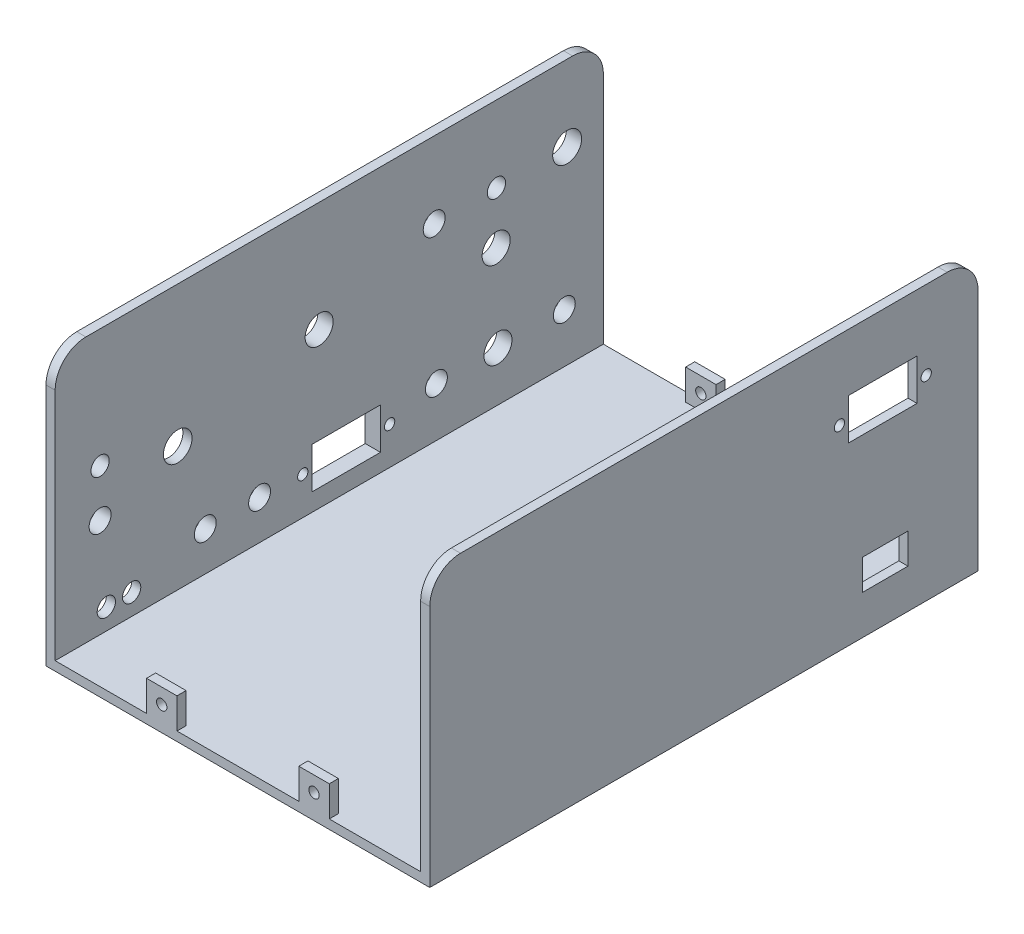
SolidWorks part; units mm, degrees
ref_plane "Front Plane" through (0, 0, 0) normal (0, 0, 1) x (1, 0, 0)
ref_plane "Top Plane" through (0, 0, 0) normal (0, 1, 0) x (1, 0, 0)
ref_plane "Right Plane" through (0, 0, 0) normal (1, 0, 0) x (0, 0, -1)
sketch "Sketch1" plane through (0, 0, 0) normal (0, 0, 1) x (1, 0, 0)
  line L1 (0, 0) -> (126, 0)
  line L2 (0, 0) -> (0, -90)
  line L3 (0, -90) -> (126, -90)
  line L4 (126, 0) -> (126, -90)
  dimension "D1" = 90
  dimension "D2" = 126
extrude "Boss-Extrude1" add sketch "Sketch1" along normal blind 3
sketch "Sketch2" plane through (0, 0, 0) normal (0, 0, -1) x (-1, 0, 0)
  line L0 (-126, -90) -> (-126, 0)
  line L1 (-126, 0) -> (0, 0)
  line L2 (0, 0) -> (0, -90)
  line L3 (0, -90) -> (-3, -90)
  line L4 (0, -90) -> (-126, -90) construction
  line L5 (-3, -90) -> (-3, -3)
  line L6 (-3, -3) -> (-123, -3)
  line L7 (-123, -3) -> (-123, -90)
  line L8 (-123, -90) -> (-126, -90)
  dimension "D1" = 3
  dimension "D2" = 3
  dimension "D3" = 3
extrude "Boss-Extrude2" add sketch "Sketch2" against normal blind 177
sketch "Sketch3" plane through (0, 0, 177) normal (0, 0, 1) x (1, 0, 0)
  line L5 (0, 0) -> (126, 0)
  line L6 (0, 0) -> (0, -90)
  line L7 (0, -90) -> (126, -90)
  line L8 (126, 0) -> (126, -90)
extrude "Boss-Extrude3" add sketch "Sketch3" along normal blind 3
fillet "Fillet1" radius 10 4 edges at (63, -3, 177) (63, 0, 180) (63, -3, 3) (63, 0, 0)
sketch "Sketch4" plane through (0, 0, 0) normal (-1, 0, 0) x (0, 0, 1)
  line L0 (0, -10) -> (0, -90) construction
  line L1 (60, -60) -> (10, -60)
  line L2 (60, -60) -> (60, -10)
  line L3 (60, -10) -> (10, -10)
  line L4 (10, -60) -> (10, -10)
  line L5 (10, -65) -> (60, -65)
  line L6 (10, -65) -> (10, -80)
  line L7 (10, -80) -> (60, -80)
  line L8 (60, -65) -> (60, -80)
  line L9 (70, -10) -> (120, -10)
  line L10 (70, -10) -> (70, -60)
  line L11 (70, -60) -> (120, -60)
  line L12 (120, -10) -> (120, -60)
  line L13 (70, -65) -> (100, -65)
  line L14 (70, -65) -> (70, -80)
  line L15 (70, -80) -> (100, -80)
  line L16 (100, -65) -> (100, -80)
  line L17 (105, -65) -> (120, -65)
  line L18 (105, -65) -> (105, -80)
  line L19 (105, -80) -> (120, -80)
  line L20 (120, -65) -> (120, -80)
  line L21 (135, -10) -> (165, -10)
  line L22 (135, -10) -> (135, -23.8915)
  line L23 (135, -23.8915) -> (165, -23.8915)
  line L24 (165, -10) -> (165, -23.8915)
  line L25 (130, -30.8764) -> (167, -30.8764)
  line L26 (130, -30.8764) -> (130, -55.8764)
  line L27 (130, -55.8764) -> (167, -55.8764)
  line L28 (167, -30.8764) -> (167, -55.8764)
  line L35 (170, 0) -> (10, 0) construction
  line L36 (180, -90) -> (0, -90) construction
  line L37 (180, -10) -> (180, -90) construction
  point P33 (135, -16.9458)
  dimension "D1" = 50
  dimension "D2" = 50
  dimension "D3" = 50
  dimension "D4" = 50
  dimension "D5" = 50
  dimension "D6" = 30
  dimension "D7" = 15
  dimension "D8" = 37
  dimension "D9" = 10
  dimension "D10" = 10
  dimension "D11" = 15
  dimension "D12" = 10
  dimension "D13" = 10
  dimension "D14" = 10
  dimension "D15" = 15
  dimension "D16" = 15
  dimension "D17" = 25
sketch "Sketch5" plane through (-2, 0, 0) normal (-1, 0, 0) x (0, 0, 1)
  line L0 (180, -10) -> (180, -90) construction
  circle A11 centre (154.8799, -80.1094) radius 3
  circle A12 centre (163.2002, -80.1094) radius 3
  dimension "D1" = 16.7998
extrude "Cut-Extrude1" cut sketch "Sketch5" against normal blind 5
sketch "Sketch6" plane through (126, 0, 0) normal (1, 0, 0) x (0, 0, -1)
  line L0 (0, -90) -> (0, -10) construction
  line L1 (-20, -32.3454) -> (-42.5, -32.3454)
  line L2 (-20, -32.3454) -> (-20, -18.8454)
  line L3 (-20, -18.8454) -> (-42.5, -18.8454)
  line L4 (-42.5, -32.3454) -> (-42.5, -18.8454)
  line L5 (-38, -67.1252) -> (-23, -67.1252)
  line L6 (-38, -67.1252) -> (-38, -77.1252)
  line L7 (-38, -77.1252) -> (-23, -77.1252)
  line L8 (-23, -67.1252) -> (-23, -77.1252)
  dimension "D1" = 22.5
  dimension "D2" = 13.5
  dimension "D3" = 20
  dimension "D4" = 10
  dimension "D5" = 15
  dimension "D6" = 23
extrude "Cut-Extrude2" cut sketch "Sketch6" against normal blind 3
sketch "Sketch7" plane through (0, -90, 0) normal (0, -1, 0) x (-1, 0, 0)
  line L5 (0, -180) -> (-180, -180)
  line L6 (0, -180) -> (0, 0)
  line L7 (0, 0) -> (-180, 0)
  line L8 (-180, -180) -> (-180, 0)
  dimension "D1" = 180
extrude "Boss-Extrude5" add sketch "Sketch7" against normal blind 3
sketch "Sketch8" plane through (0, 0, 0) normal (-1, 0, 0) x (0, 0, 1)
  line L0 (0, -79.8987) -> (0, -90)
  line L5 (10.1013, 0) -> (169.8987, 0)
  line L6 (0, -10.1013) -> (0, -79.8987)
  line L7 (10.1013, -90) -> (169.8987, -90)
  line L8 (180, -10.1013) -> (180, -79.8987)
  line L13 (0, -90) -> (10.1013, -90)
  line L14 (169.8987, -90) -> (180, -90)
  line L15 (180, -90) -> (180, -79.8987)
  arc A1 (10.1013, 0) -> (0, -10.1013) centre (10.1013, -10.1013) ccw
  arc A2 (169.8987, 0) -> (180, -10.1013) centre (169.8987, -10.1013) cw
  point P12 (0, 0)
  point P17 (180, -90)
extrude "Cut-Extrude3" cut sketch "Sketch8" against normal through all flip side to cut
sketch "Sketch9" plane through (0, 0, 0) normal (0, 0, -1) x (-1, 0, 0)
  line L1 (-123, 0) -> (-3, 0)
  line L2 (-123, 0) -> (-123, -87)
  line L3 (-123, -87) -> (-3, -87)
  line L4 (-3, 0) -> (-3, -87)
  line L5 (-126, -87) -> (-126, -10.1013) construction
  line L6 (0, -10.1013) -> (0, -90) construction
  line L7 (-180, -90) -> (0, -90) construction
  dimension "D1" = 3
  dimension "D2" = 3
  dimension "D3" = 3
  dimension "D4" = 87
extrude "Cut-Extrude4" cut sketch "Sketch9" against normal through all
sketch "Sketch11" plane through (0, -87, 0) normal (0, 1, 0) x (1, 0, 0)
  line L0 (123, -180) -> (3, -180) construction
  line L9 (33, -180) -> (43, -180)
  line L10 (33, -180) -> (33, -177)
  line L11 (33, -177) -> (43, -177)
  line L12 (43, -180) -> (43, -177)
  line L13 (123, 0) -> (3, 0) construction
  line L14 (83, -180) -> (93, -180)
  line L15 (83, -180) -> (83, -177)
  line L16 (83, -177) -> (93, -177)
  line L17 (93, -180) -> (93, -177)
  line L18 (33, 0) -> (43, 0)
  line L19 (33, 0) -> (33, -3)
  line L20 (33, -3) -> (43, -3)
  line L21 (43, 0) -> (43, -3)
  line L22 (3, -180) -> (3, 0) construction
  line L23 (83, 0) -> (93, 0)
  line L24 (83, 0) -> (83, -3)
  line L25 (83, -3) -> (93, -3)
  line L26 (93, 0) -> (93, -3)
  line L27 (123, 0) -> (123, -180) construction
  point P20 (43, -178.5)
  point P23 (93, -178.5)
  dimension "D1" = 3
  dimension "D2" = 3
  dimension "D3" = 3
  dimension "D4" = 3
  dimension "D5" = 10
  dimension "D6" = 10
  dimension "D7" = 10
  dimension "D8" = 10
  dimension "D9" = 30
  dimension "D10" = 30
  dimension "D11" = 40
  dimension "D12" = 30
  dimension "D13" = 30
extrude "Boss-Extrude6" add sketch "Sketch11" along normal blind 10
sketch "Sketch12" plane through (0, 0, 0) normal (0, 0, -1) x (-1, 0, 0)
  line L0 (-93, -77) -> (-93, -87) construction
  line L1 (-93, -77) -> (-83, -77) construction
  line L2 (-43, -77) -> (-43, -87) construction
  line L3 (-43, -77) -> (-33, -77) construction
  circle A1 centre (-88, -82) radius 1.7
  circle A2 centre (-38, -82) radius 1.7
  dimension "D1" = 5
  dimension "D2" = 5
  dimension "D3" = 5
  dimension "D4" = 5
extrude "Cut-Extrude5" cut sketch "Sketch12" against normal blind 10
sketch "Sketch13" plane through (0, 0, 180) normal (0, 0, 1) x (1, 0, 0)
  line L0 (33, -77) -> (33, -87) construction
  line L1 (33, -77) -> (43, -77) construction
  line L2 (83, -77) -> (83, -87) construction
  line L3 (83, -77) -> (93, -77) construction
  circle A0 centre (38, -82) radius 1.7
  circle A1 centre (88, -82) radius 1.7
  dimension "D1" = 5
  dimension "D2" = 5
  dimension "D3" = 5
  dimension "D4" = 5
extrude "Cut-Extrude6" cut sketch "Sketch13" against normal blind 10
sketch "Sketch14" plane through (3, 0, 0) normal (1, 0, 0) x (0, 0, -1)
  line L1 (-42.6204, -21) -> (-27.6204, -21) construction
  line L2 (-42.6204, -21) -> (-42.6204, -29) construction
  line L3 (-42.6204, -29) -> (-27.6204, -29) construction
  line L4 (-27.6204, -21) -> (-27.6204, -29) construction
  line L5 (-50.7016, -29.5503) -> (-19.7016, -29.5503) construction
  line L6 (-50.7016, -29.5503) -> (-50.7016, -54.5503) construction
  line L7 (-50.7016, -54.5503) -> (-19.7016, -54.5503) construction
  line L8 (-19.7016, -29.5503) -> (-19.7016, -54.5503) construction
  line L9 (-46.3264, -55.2522) -> (-21.3264, -55.2522) construction
  line L10 (-46.3264, -55.2522) -> (-46.3264, -86.2522) construction
  line L11 (-46.3264, -86.2522) -> (-21.3264, -86.2522) construction
  line L12 (-21.3264, -55.2522) -> (-21.3264, -86.2522) construction
  line L13 (-42.6204, -21) -> (-27.6204, -21)
  line L14 (-42.6204, -21) -> (-42.6204, -29)
  line L15 (-42.6204, -29) -> (-27.6204, -29)
  line L16 (-27.6204, -21) -> (-27.6204, -29)
  line L17 (-46.3264, -55.2522) -> (-21.3264, -55.2522)
  line L18 (-46.3264, -55.2522) -> (-46.3264, -86.2522)
  line L19 (-46.3264, -86.2522) -> (-21.3264, -86.2522)
  line L20 (-21.3264, -55.2522) -> (-21.3264, -86.2522)
  line L21 (-50.7016, -29.5503) -> (-19.7016, -29.5503)
  line L22 (-50.7016, -29.5503) -> (-50.7016, -54.5503)
  line L23 (-50.7016, -54.5503) -> (-19.7016, -54.5503)
  line L24 (-19.7016, -29.5503) -> (-19.7016, -54.5503)
  line L25 (-172.7432, -34.9908) -> (-157.7432, -34.9908)
  line L26 (-172.7432, -34.9908) -> (-172.7432, -42.9908)
  line L27 (-172.7432, -42.9908) -> (-157.7432, -42.9908)
  line L28 (-157.7432, -34.9908) -> (-157.7432, -42.9908)
  line L34 (-73.1878, -67.6661) -> (-95.6878, -67.6661)
  line L35 (-73.1878, -67.6661) -> (-73.1878, -81.1661)
  line L36 (-73.1878, -81.1661) -> (-95.6878, -81.1661)
  line L37 (-95.6878, -67.6661) -> (-95.6878, -81.1661)
  line L38 (-180, -90) -> (0, -90) construction
  line L39 (-105.8166, -20.6885) -> (-80.8166, -20.6885)
  line L40 (-105.8166, -20.6885) -> (-105.8166, -51.6885)
  line L41 (-105.8166, -51.6885) -> (-80.8166, -51.6885)
  line L42 (-80.8166, -20.6885) -> (-80.8166, -51.6885)
  line L43 (-103.1878, -66.9931) -> (-65.1878, -66.9931)
  line L44 (-103.1878, -66.9931) -> (-103.1878, -81.9931)
  line L45 (-103.1878, -81.9931) -> (-65.1878, -81.9931)
  line L46 (-65.1878, -66.9931) -> (-65.1878, -81.9931)
  line L47 (0, -87) -> (0, -10.1013) construction
  circle A1 centre (-11.8978, -25) radius 11.25 construction
  circle A2 centre (-55.5472, -25) radius 8.5 construction
  circle A3 centre (-12.8264, -70.7522) radius 8.5 construction
  circle A4 centre (-54.8264, -70.7522) radius 8.5 construction
  circle A5 centre (-11.8978, -25) radius 11.1
  circle A6 centre (-55.5472, -25) radius 8.5
  circle A7 centre (-54.8264, -70.7522) radius 8.5
  circle A8 centre (-12.8264, -70.7522) radius 8.5
  circle A9 centre (-112.8727, -74.1268) radius 8.5
  circle A10 centre (-130.7113, -74.1268) radius 8.5
  circle A11 centre (-165.2432, -54.5503) radius 8.5
  circle A12 centre (-139.7536, -46.1677) radius 11.15
  point P78 (-165.2432, -42.9908)
  dimension "D1" = 15
  dimension "D3" = 17
  dimension "D8" = 38
  dimension "D13" = 15
  dimension "D20" = 22.2
  dimension "D21" = 17
  dimension "D22" = 17
  dimension "D23" = 22.3
  dimension "D24" = 17
  dimension "D25" = 17
  dimension "D26" = 17
  dimension "D27" = 17
  dimension "D2" = 8
  dimension "D4" = 31
  dimension "D5" = 25
  dimension "D6" = 31
  dimension "D7" = 25
  dimension "D9" = 7.5
  dimension "D10" = 25
  dimension "D11" = 21
  dimension "D12" = 15
  dimension "D14" = 8
  dimension "D15" = 22.5
  dimension "D16" = 13.5
  dimension "D17" = 3.7478
  dimension "D18" = 25
  dimension "D19" = 31
  dimension "D28" = 15.5
  dimension "D29" = 12.8264
  dimension "D30" = 8.5
  dimension "D31" = 8.5
sketch "Sketch16" plane through (-2, 0, 0) normal (-1, 0, 0) x (0, 0, 1)
  line L0 (0, -10.1013) -> (0, -90) construction
  line L5 (3.3978, -7) -> (63.3978, -7)
  line L6 (3.3978, -7) -> (3.3978, -52)
  line L7 (3.3978, -52) -> (63.3978, -52)
  line L8 (63.3978, -7) -> (63.3978, -52)
  line L9 (6.25, -55) -> (61.3865, -55)
  line L10 (6.25, -55) -> (6.25, -85)
  line L11 (6.25, -85) -> (61.3865, -85)
  line L12 (61.3865, -55) -> (61.3865, -85)
  line L13 (68.5355, -8) -> (118.5355, -8)
  line L14 (68.5355, -8) -> (68.5355, -53)
  line L15 (68.5355, -53) -> (118.5355, -53)
  line L16 (118.5355, -8) -> (118.5355, -53)
  line L17 (63.1467, -55) -> (120.8778, -55)
  line L18 (63.1467, -55) -> (63.1467, -85)
  line L19 (63.1467, -85) -> (120.8778, -85)
  line L20 (120.8778, -55) -> (120.8778, -85)
  line L21 (123.3103, -54.9622) -> (137.9052, -54.9622)
  line L22 (123.3103, -54.9622) -> (123.3103, -84.9622)
  line L23 (123.3103, -84.9622) -> (137.9052, -84.9622)
  line L24 (137.9052, -54.9622) -> (137.9052, -84.9622)
  line L25 (152.6969, -26.1054) -> (177.6096, -26.1054)
  line L26 (152.6969, -26.1054) -> (152.6969, -62.5896)
  line L27 (152.6969, -62.5896) -> (177.6096, -62.5896)
  line L28 (177.6096, -26.1054) -> (177.6096, -62.5896)
  line L29 (180, -90) -> (0, -90) construction
  line L30 (169.8987, 0) -> (10.1013, 0) construction
  circle A1 centre (11.8978, -25) radius 11.25 construction
  point P12 (130.6078, -84.9622)
  dimension "D1" = 60
  dimension "D2" = 8.5
  dimension "D3" = 6.25
  dimension "D4" = 55
  dimension "D5" = 5
  dimension "D6" = 5
  dimension "D7" = 45
  dimension "D8" = 30
  dimension "D9" = 50
  dimension "D10" = 45
  dimension "D11" = 7
  dimension "D12" = 8
  dimension "D13" = 30
extrude "Boss-Extrude7" add sketch "Sketch16" against normal blind 5
sketch "Sketch15" plane through (-2, 0, 0) normal (-1, 0, 0) x (0, 0, 1)
  line L0 (46.3264, -86.2522) -> (21.3264, -86.2522) construction
  line L1 (27.6204, -21) -> (27.6204, -29) construction
  line L2 (73.1878, -67.6661) -> (95.6878, -67.6661)
  line L3 (73.1878, -67.6661) -> (73.1878, -81.1661)
  line L4 (73.1878, -81.1661) -> (95.6878, -81.1661)
  line L5 (95.6878, -67.6661) -> (95.6878, -81.1661)
  line L10 (19.7016, -29.5503) -> (19.7016, -54.5503) construction
  line L11 (50.7016, -54.5503) -> (19.7016, -54.5503) construction
  line L13 (80.8166, -20.6885) -> (80.8166, -51.6885) construction
  line L14 (172.7432, -42.9908) -> (157.7432, -42.9908) construction
  line L16 (157.7432, -34.9908) -> (157.7432, -42.9908) construction
  circle A0 centre (11.8978, -25) radius 4.75
  circle A1 centre (35.1204, -25) radius 3
  circle A2 centre (55.5472, -25) radius 3.6
  circle A3 centre (93.3166, -36.1885) radius 4.6
  circle A4 centre (12.8264, -70.7522) radius 3.6
  circle A5 centre (54.8264, -70.7522) radius 3.6
  circle A6 centre (34.6032, -70.7522) radius 4.6
  circle A7 centre (35.2016, -42.0503) radius 4.6
  circle A8 centre (112.8727, -74.1268) radius 3.6
  circle A9 centre (130.7113, -74.1268) radius 3.6
  circle A10 centre (139.7536, -46.1677) radius 4.7
  circle A11 centre (165.2432, -54.5503) radius 3.6
  circle A12 centre (165.2432, -38.9908) radius 3
  circle A14 centre (11.8978, -25) radius 11.1 construction
  circle A15 centre (55.5472, -25) radius 8.5 construction
  circle A16 centre (12.8264, -70.7522) radius 8.5 construction
  circle A17 centre (54.8264, -70.7522) radius 8.5 construction
  circle A18 centre (112.8727, -74.1268) radius 8.5 construction
  circle A19 centre (130.7113, -74.1268) radius 8.5 construction
  circle A20 centre (139.7536, -46.1677) radius 11.15 construction
  circle A21 centre (165.2432, -54.5503) radius 8.5 construction
  point P48 (27.6204, -25)
  point P54 (19.7016, -42.0503)
  point P78 (80.8166, -36.1885)
  dimension "D1" = 7.2
  dimension "D2" = 13.5
  dimension "D3" = 15.5
  dimension "D4" = 12.5
  dimension "D5" = 15.5
  dimension "D6" = 12.5
  dimension "D7" = 4
  dimension "D8" = 7.5
  dimension "D11" = 21.7768
  dimension "D12" = 20.2232
extrude "Cut-Extrude7" cut sketch "Sketch15" against normal mid plane 15
fillet "Fillet3" radius 2.27 24 edges at (-1, -26.1054, 152.6969) (-1, -26.1054, 177.6096) (-1, -62.5896, 177.6096) (-1, -62.5896, 152.6969) (-1, -84.9622, 123.3103) (-1, -84.9622, 137.9052) (-1, -54.9622, 123.3103) (-1, -54.9622, 137.9052) (-1, -55, 120.8778) (-1, -85, 120.8778) (-1, -85, 63.1467) (-1, -85, 61.3865) (-1, -85, 6.25) (-1, -55, 6.25) (-1, -55, 63.1467) (-1, -55, 61.3865) (-1, -52, 63.3978) (-1, -52, 3.3978) (-1, -53, 68.5355) (-1, -53, 118.5355) (-1, -8, 118.5355) (-1, -8, 68.5355) (-1, -7, 63.3978) (-1, -7, 3.3978)
sketch "Sketch17" plane through (0, -87, 0) normal (0, 1, 0) x (1, 0, 0)
  line L1 (126, 0) -> (180, 0)
  line L2 (126, 0) -> (126, -180)
  line L3 (126, -180) -> (180, -180)
  line L4 (180, 0) -> (180, -180)
extrude "Cut-Extrude8" cut sketch "Sketch17" against normal blind 10
sketch "Sketch18" plane through (0, 0, 0) normal (-1, 0, 0) x (0, 0, 1)
  line L0 (180, -10.1013) -> (180, -90) construction
  line L5 (129, -5) -> (171, -5)
  line L6 (125, -9) -> (125, -19)
  line L7 (129, -23) -> (171, -23)
  line L8 (175, -9) -> (175, -19)
  line L9 (169.8987, 0) -> (10.1013, 0) construction
  arc A0 (171, -23) -> (175, -19) centre (171, -19) ccw
  arc A1 (171, -5) -> (175, -9) centre (171, -9) cw
  arc A2 (125, -19) -> (129, -23) centre (129, -19) ccw
  arc A3 (129, -5) -> (125, -9) centre (129, -9) ccw
  point P10 (175, -23)
  point P13 (175, -5)
  point P18 (125, -5)
  dimension "D5" = 4
  dimension "D1" = 50
  dimension "D2" = 18
  dimension "D3" = 5
  dimension "D4" = 5
extrude "Boss-Extrude8" add sketch "Sketch18" along normal blind 2
sketch "Sketch19" plane through (-2, 0, 0) normal (-1, 0, 0) x (0, 0, 1)
  line L0 (95.6878, -81.1661) -> (95.6878, -67.6661) construction
  line L1 (73.1878, -67.6661) -> (73.1878, -81.1661) construction
  line L2 (73.1878, -81.1661) -> (95.6878, -81.1661) construction
  circle A1 centre (98.6878, -74.6661) radius 1.7
  circle A2 centre (70.1878, -74.6661) radius 1.7
  dimension "D1" = 3.4
  dimension "D2" = 3.4
  dimension "D3" = 3
  dimension "D4" = 3
  dimension "D5" = 6.5
  dimension "D6" = 6.5
extrude "Cut-Extrude9" cut sketch "Sketch19" against normal blind 12
sketch "Sketch20" plane through (126, 0, 0) normal (1, 0, 0) x (0, 0, -1)
  line L0 (-20, -32.3454) -> (-20, -18.8454) construction
  line L1 (-42.5, -18.8454) -> (-42.5, -32.3454) construction
  line L2 (-42.5, -32.3454) -> (-20, -32.3454) construction
  circle A0 centre (-17, -25.8454) radius 1.7
  circle A1 centre (-45.5, -25.8454) radius 1.7
  dimension "D1" = 3.4
  dimension "D2" = 3.4
  dimension "D3" = 3
  dimension "D4" = 3
  dimension "D5" = 6.5
  dimension "D6" = 6.5
extrude "Cut-Extrude10" cut sketch "Sketch20" against normal blind 12
